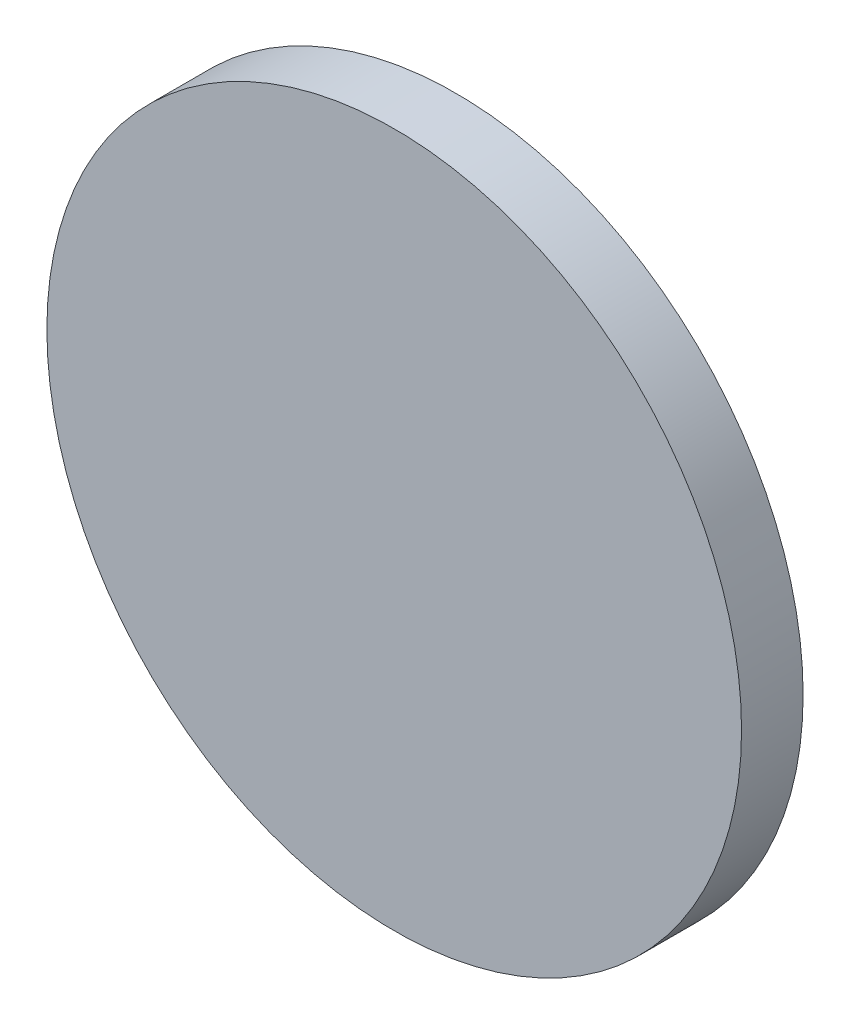
SolidWorks part; units mm, degrees
ref_plane "Front Plane" through (0, 0, 0) normal (0, 0, 1) x (1, 0, 0)
ref_plane "Top Plane" through (0, 0, 0) normal (0, 1, 0) x (1, 0, 0)
ref_plane "Right Plane" through (0, 0, 0) normal (1, 0, 0) x (0, 0, -1)
sketch "Sketch1" plane through (0, 0, 0) normal (0, 0, 1) x (1, 0, 0)
  circle A0 centre (0, 0) radius 14.3273
extrude "Boss-Extrude1" add sketch "Sketch1" along normal blind 2.54
